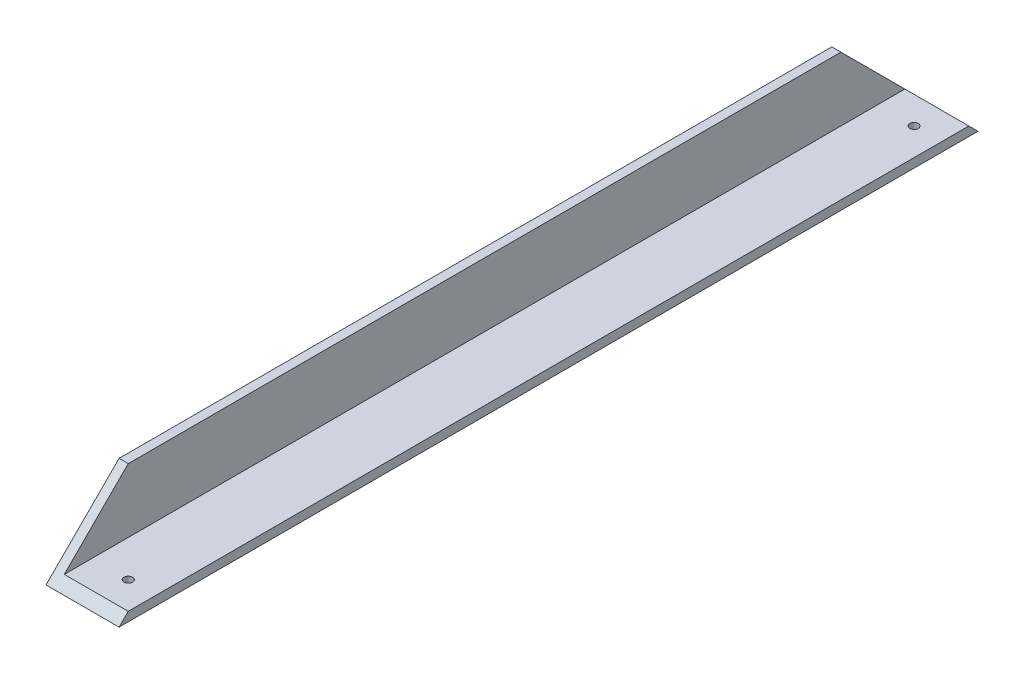
SolidWorks part; units mm, degrees
material "1060-O (SS)"
ref_plane "Front Plane" through (0, 0, 0) normal (0, 0, 1) x (1, 0, 0)
ref_plane "Top Plane" through (0, 0, 0) normal (0, 1, 0) x (1, 0, 0)
ref_plane "Right Plane" through (0, 0, 0) normal (1, 0, 0) x (0, 0, -1)
sketch "Sketch1" plane through (0, 0, 0) normal (0, 0, 1) x (1, 0, 0)
  line L0 (0, 0) -> (0, 34.0895) construction
  line L1 (0, 0) -> (36.0947, 0) construction
  line L2 (0, 25.4) -> (0, 0)
  line L3 (0, 0) -> (25.4, 0)
  line L4 (25.4, 0) -> (25.4, 3.175)
  line L5 (25.4, 3.175) -> (3.175, 3.175)
  line L6 (3.175, 3.175) -> (3.175, 25.4)
  line L7 (3.175, 25.4) -> (0, 25.4)
  dimension "D1" = 25.4
  dimension "D2" = 25.4
  dimension "D3" = 3.175
  dimension "D4" = 3.175
extrude "Boss-Extrude1" add sketch "Sketch1" along normal blind 298.45
sketch "Sketch2" plane through (0, 0, 0) normal (-1, 0, 0) x (0, 0, 1)
  line L0 (0, 0) -> (25.4, 25.4)
  line L1 (298.45, 25.4) -> (0, 25.4) construction
  line L2 (298.45, 0) -> (273.05, 25.4)
  line L3 (0, 0) -> (0, 8.5421)
  line L4 (0, 25.4) -> (0, 0) construction
  line L5 (0, 25.4) -> (25.4, 25.4)
  line L6 (273.05, 25.4) -> (298.45, 25.4)
  line L7 (298.45, 25.4) -> (298.45, 0)
  line M3 (0, 25.4) -> (0, 0)
  line M5 (298.45, 0) -> (298.45, 25.4)
  line M6 (298.45, 25.4) -> (0, 25.4)
  dimension "D1" = 25.4
  dimension "D2" = 25.4
extrude "Cut-Extrude1" cut sketch "Sketch2" against normal blind 711.2 contours L0 M3 M6 | L2 M5 M6
sketch "Sketch3" plane through (0, 0, 0) normal (0, -1, 0) x (1, 0, 0)
  line L0 (0, 0) -> (25.4, 0) construction
  line L1 (0, 298.45) -> (25.4, 298.45) construction
  line L3 (25.4, 298.45) -> (25.4, 0) construction
  circle A0 centre (15.875, 285.75) radius 1.5
  circle A1 centre (15.875, 12.7) radius 1.5
  dimension "D1" = 3
  dimension "D2" = 3
  dimension "D3" = 12.7
  dimension "D4" = 12.7
  dimension "D5" = 9.525
  dimension "D6" = 9.525
extrude "Cut-Extrude2" cut sketch "Sketch3" against normal blind 711.2
